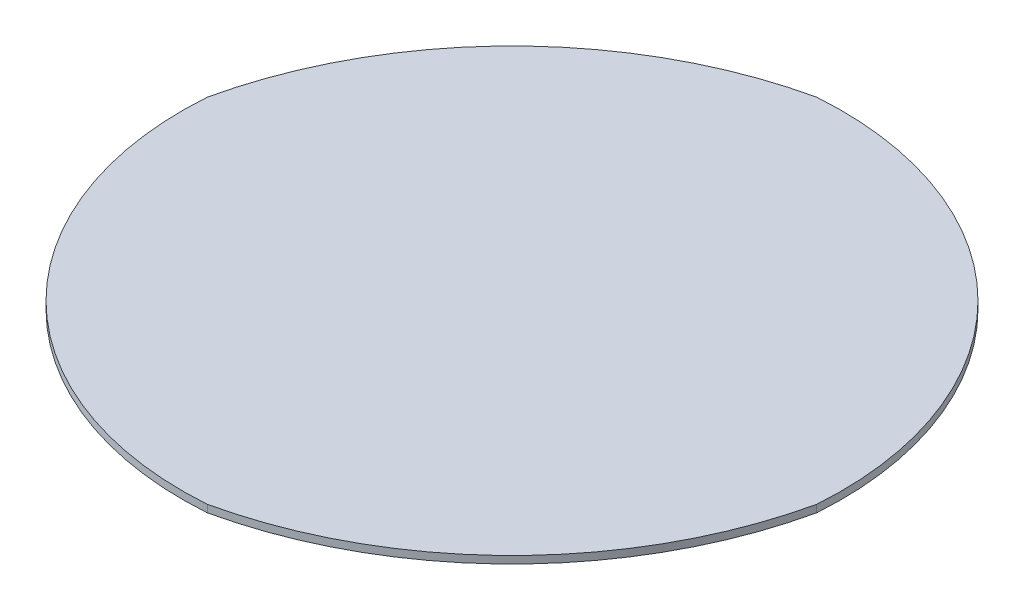
SolidWorks part; units mm, degrees
ref_plane "Front Plane" through (0, 0, 0) normal (0, 0, 1) x (1, 0, 0)
ref_plane "Top Plane" through (0, 0, 0) normal (0, 1, 0) x (1, 0, 0)
ref_plane "Right Plane" through (0, 0, 0) normal (1, 0, 0) x (0, 0, -1)
sketch "Sketch1" plane through (0, 0, 0) normal (0, 1, 0) x (1, 0, 0)
  line L0 (0, 0) -> (17.0743, 17.0743)
  line L1 (-148.8075, 41.6346) -> (-90, 0)
  line L2 (-148.8075, 41.6346) -> (-57.6282, 163.6658)
  line L3 (-57.6282, 163.6658) -> (0, 90)
  line L4 (90, 0) -> (186.2475, -76.1859)
  line L5 (186.2475, -76.1859) -> (27.0223, -178.4501)
  line L6 (27.0223, -178.4501) -> (0, -90)
  arc A1 (0, 90) -> (-90, 0) centre (17.0743, -17.0743) ccw
  arc A2 (90, 0) -> (0, -90) centre (-17.0743, 17.0743) cw
sketch "Sketch2" plane through (0, 0, 0) normal (0, 1, 0) x (1, 0, 0)
  circle A0 centre (0, 0) radius 89
extrude "Boss-Extrude1" add sketch "Sketch2" along normal blind 2 contours A0
extrude "Cut-Extrude2" cut sketch "Sketch1" against normal blind 22 and the other way blind 2 contours L4 A2 L6 L5 | A1 L3 L2 L1
